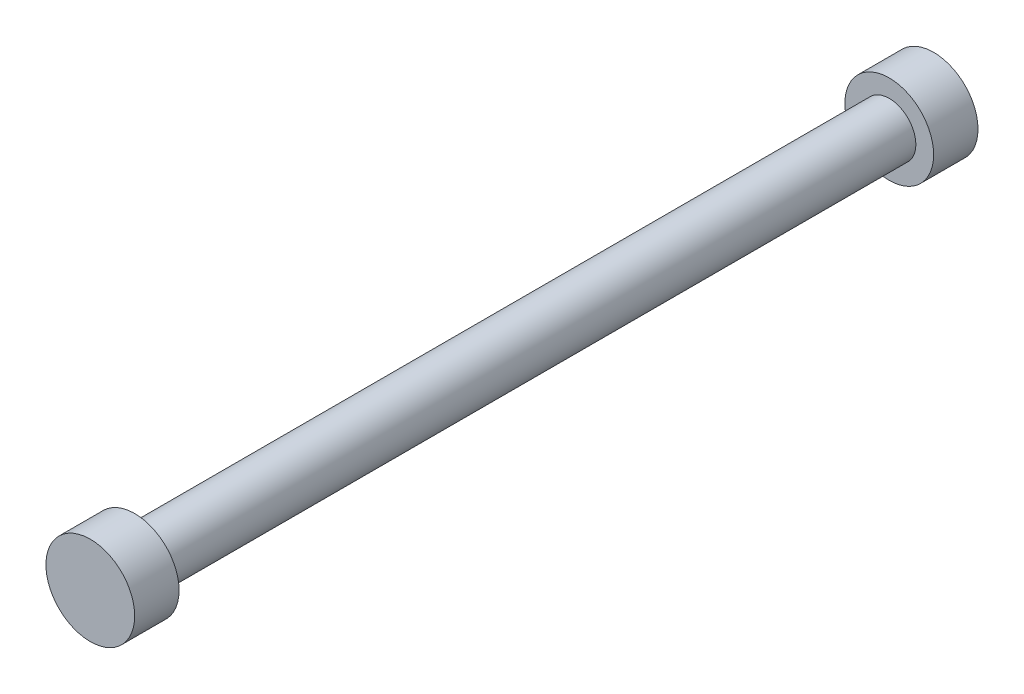
SolidWorks part; units mm, degrees
ref_plane "Front Plane" through (0, 0, 0) normal (0, 0, 1) x (1, 0, 0)
ref_plane "Top Plane" through (0, 0, 0) normal (0, 1, 0) x (1, 0, 0)
ref_plane "Right Plane" through (0, 0, 0) normal (1, 0, 0) x (0, 0, -1)
sketch "Sketch1" plane through (0, 0, 0) normal (0, 0, 1) x (1, 0, 0)
  circle A0 centre (0, 0) radius 3
  dimension "D1" = 6
extrude "Boss-Extrude1" add sketch "Sketch1" along normal mid plane 85
sketch "Sketch2" plane through (0, 0, 42.5) normal (0, 0, 1) x (1, 0, 0)
  circle A0 centre (0, 0) radius 5
  dimension "D1" = 10
extrude "Boss-Extrude2" add sketch "Sketch2" along normal blind 5
mirror "Mirror1" about plane through (0, 0, 0) normal (0, 0, 1) of "Boss-Extrude2"
